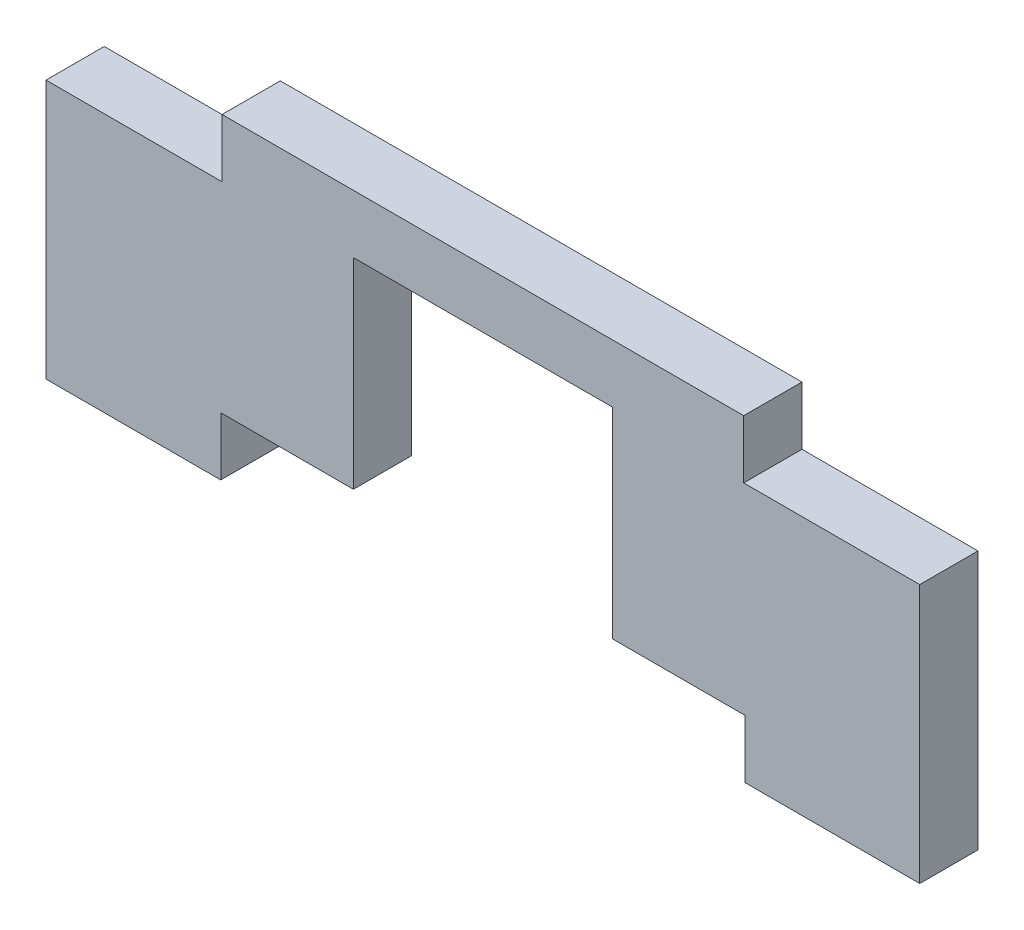
SolidWorks part; units mm, degrees
ref_plane "Front Plane" through (0, 0, 0) normal (0, 0, 1) x (1, 0, 0)
ref_plane "Top Plane" through (0, 0, 0) normal (0, 1, 0) x (1, 0, 0)
ref_plane "Right Plane" through (0, 0, 0) normal (1, 0, 0) x (0, 0, -1)
sketch "Sketch1" plane through (0, 0, 232.248) normal (0, 0, 1) x (1, 0, 0)
  line L0 (-82.2575, 116.9148) -> (-82.2575, 82.4648)
  line L1 (-82.2575, 82.4648) -> (-82.2575, 72.4648)
  line L3 (-82.2575, 72.4648) -> (-52.2575, 72.4648)
  line L5 (-52.2575, 72.4648) -> (-52.2575, 82.4648)
  line L6 (-82.2575, 82.4648) -> (-29.4825, 82.4648) construction
  line L7 (-52.2575, 82.4648) -> (-29.4825, 82.4648)
  line L8 (-29.4825, 82.4648) -> (-29.4825, 116.9148)
  line L9 (-52.0369, 126.9148) -> (37.522, 126.9148)
  line L11 (280.006, 122.4648) -> (-294.5209, 122.4648) construction
  line L12 (-29.4825, 116.9148) -> (14.9675, 116.9148)
  line L13 (-52.0369, 126.9148) -> (-52.0369, 116.9148)
  line L14 (-52.0369, 116.9148) -> (-82.2575, 116.9148)
  line L15 (37.7425, 82.4648) -> (14.9675, 82.4648)
  line L16 (-7.2575, 111.3889) -> (-7.2575, 148.6392) construction
  line L17 (-29.4825, 111.3889) -> (14.9675, 111.3889) construction
  line L18 (37.522, 116.9148) -> (67.7425, 116.9148)
  line L19 (37.522, 126.9148) -> (37.522, 116.9148)
  line L20 (14.9675, 82.4648) -> (14.9675, 116.9148)
  line L21 (37.7425, 72.4648) -> (37.7425, 82.4648)
  line L22 (67.7425, 82.4648) -> (67.7425, 72.4648)
  line L23 (67.7425, 72.4648) -> (37.7425, 72.4648)
  line L24 (-29.4825, 116.9148) -> (14.9675, 116.9148) construction
  line L26 (67.7425, 116.9148) -> (67.7425, 82.4648)
  line L27 (16.1124, 116.9148) -> (-30.6274, 116.9148) construction
  point P28 (-7.2575, 122.4648)
  point P32 (-7.2575, 116.9148)
  dimension "D1" = 30
  dimension "D2" = 10
  dimension "D3" = 45
  dimension "D4" = 10
extrude "Boss-Extrude1" add sketch "Sketch1" against normal blind 10
